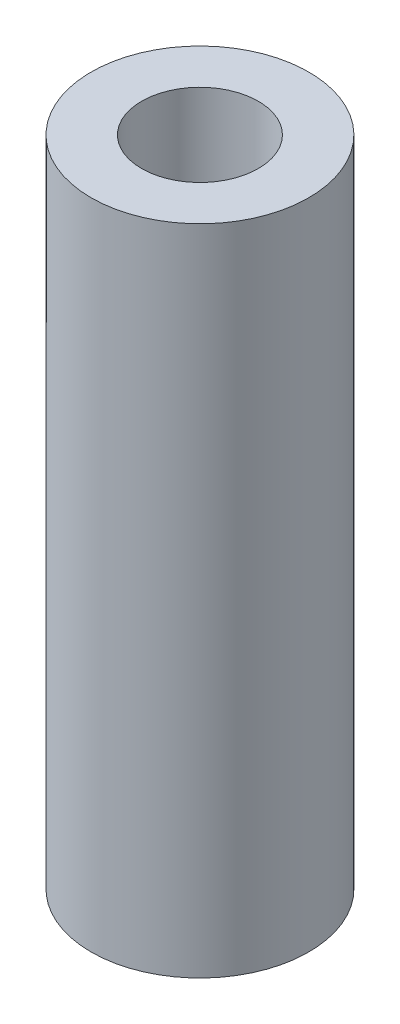
SolidWorks part; units mm, degrees
material "6061-T6 (SS)"
ref_plane "Front Plane" through (0, 0, 0) normal (0, 0, 1) x (1, 0, 0)
ref_plane "Top Plane" through (0, 0, 0) normal (0, 1, 0) x (1, 0, 0)
ref_plane "Right Plane" through (0, 0, 0) normal (1, 0, 0) x (0, 0, -1)
sketch "Sketch1" plane through (0, 0, 0) normal (0, 1, 0) x (1, 0, 0)
  circle A0 centre (0, 0) radius 2.5527
  circle A1 centre (0, 0) radius 4.7625
  dimension "D1" = 5.1054
  dimension "D2" = 9.525
extrude "Boss-Extrude1" add sketch "Sketch1" along normal mid plane 28.575
